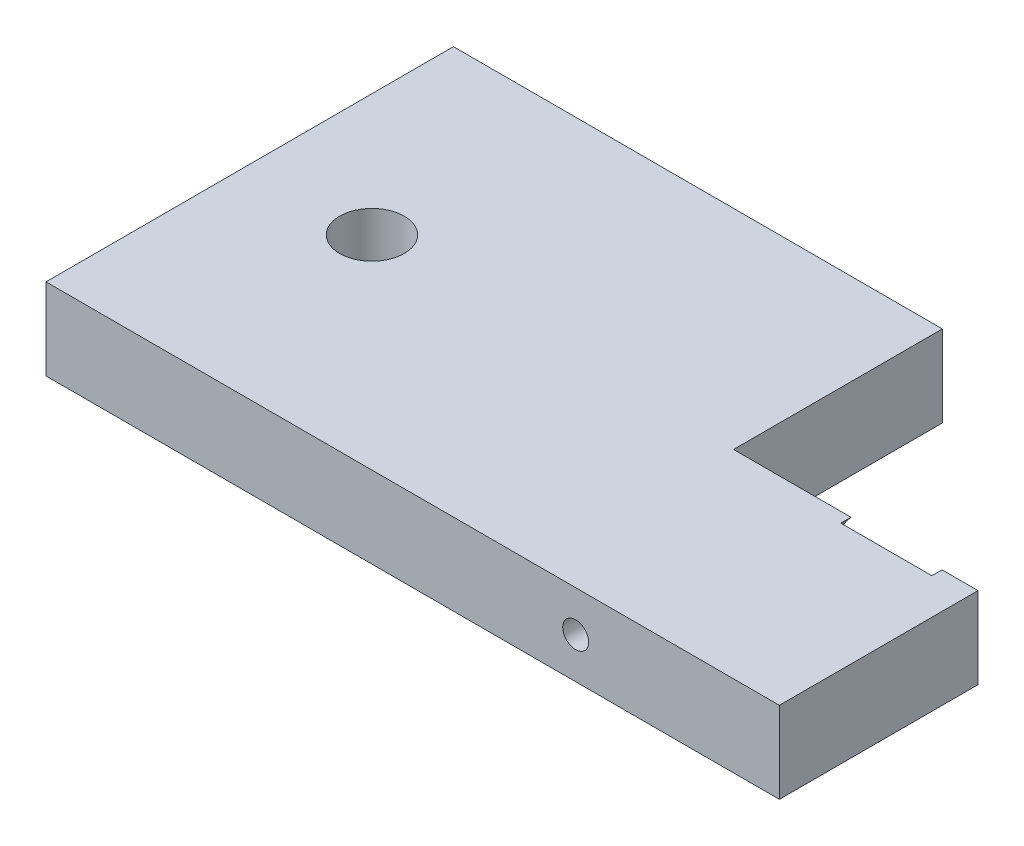
SolidWorks part; units mm, degrees
material "6061-T6 (SS)"
ref_plane "Front Plane" through (0, 0, 0) normal (0, 0, 1) x (1, 0, 0)
ref_plane "Top Plane" through (0, 0, 0) normal (0, 1, 0) x (1, 0, 0)
ref_plane "Right Plane" through (0, 0, 0) normal (1, 0, 0) x (0, 0, -1)
sketch "Sketch1" plane through (0, 0, 0) normal (0, 1, 0) x (1, 0, 0)
  line L0 (-114.3, 31.75) -> (-114.3, -0.7937)
  line L1 (-114.3, 31.75) -> (190.5, 31.75) construction
  line L2 (-190.5, 31.75) -> (-190.5, -31.75)
  line L3 (-76.2, -31.75) -> (190.5, -31.75) construction
  line L4 (190.5, 31.75) -> (190.5, -31.75) construction
  line L5 (-190.5, 31.75) -> (190.5, -31.75) construction
  line L6 (-190.5, -31.75) -> (190.5, 31.75) construction
  line L7 (-114.3, -0.7937) -> (-76.2, -0.7937)
  line L8 (-76.2, -0.7937) -> (-76.2, -31.75)
  line L9 (-190.5, 31.75) -> (-114.3, 31.75)
  line L10 (-190.5, -31.75) -> (-76.2, -31.75)
  point P0 (0, 0)
  dimension "D1" = 381
  dimension "D2" = 63.5
  dimension "D3" = 0.7937
  dimension "D4" = 38.1
  dimension "D5" = 76.2
extrude "Boss-Extrude1" add sketch "Sketch1" along normal blind 12.7
hole_wizard "#10-32 Tapped Hole1" positions "Sketch5" profile "Sketch6" tap size "#10-32" standard "ANSI Inch" end condition through all
sketch "Sketch5" plane through (0, 0, 0.7937) normal (0, 0, -1) x (-1, 0, 0)
  line L3 (107.95, 6.35) -> (114.3, 12.7) construction
  line L5 (107.95, 6.35) -> (114.3, 0) construction
  line L7 (114.3, 12.7) -> (114.3, 0) construction
  point P0 (107.95, 6.35)
  dimension "D1" = 6.35
sketch "Sketch6" plane through (-107.95, 6.35, 0.7937) normal (1, 0, 0) x (0, 1, 0)
  line L0 (0, 0) -> (0, 30.9563)
  line L1 (0, 30.9563) -> (2.0193, 30.9563)
  line L2 (2.0193, 30.9563) -> (2.0193, 0)
  line L5 (2.0193, 0) -> (0, 0)
  line L11 (0, -6.35) -> (0, 107.95) construction
  dimension "Thread Major Dia." = 4.0386
  dimension "Thru Tap Drill Depth" = 30.9563
hole_wizard "3/8 Clearance Hole1" positions "Sketch7" profile "Sketch8" hole size "3/8" standard "ANSI Inch" end condition through all
sketch "Sketch7" plane through (0, 12.7, 0) normal (0, 1, 0) x (1, 0, 0)
  line L0 (-190.5, 31.75) -> (-190.5, -31.75) construction
  point P0 (-171.45, 0)
  dimension "D1" = 19.05
sketch "Sketch8" plane through (-171.45, 12.7, 0) normal (1, 0, 0) x (0, 0, 1)
  line L0 (0, 0) -> (0, 12.7)
  line L1 (0, 12.7) -> (5.0419, 12.7)
  line L2 (5.0419, 12.7) -> (5.0419, 0)
  line L5 (5.0419, 0) -> (0, 0)
  line L11 (0, -6.35) -> (0, 107.95) construction
  dimension "Thru Hole Dia." = 10.0838
  dimension "Thru Hole Depth" = 12.7
sketch "Sketch9" plane through (0, 0, 0.7937) normal (0, 0, -1) x (-1, 0, 0)
  line L0 (76.2, 12.7) -> (76.2, 0) construction
  line L1 (76.2, 12.7) -> (88.9, 6.35) construction
  line L2 (88.9, 6.35) -> (76.2, 0) construction
  circle A0 centre (88.9, 6.35) radius 9.525
  dimension "D1" = 19.05
  dimension "D2" = 12.7
extrude "Cut-Extrude1" cut sketch "Sketch9" against normal blind 1.5875
